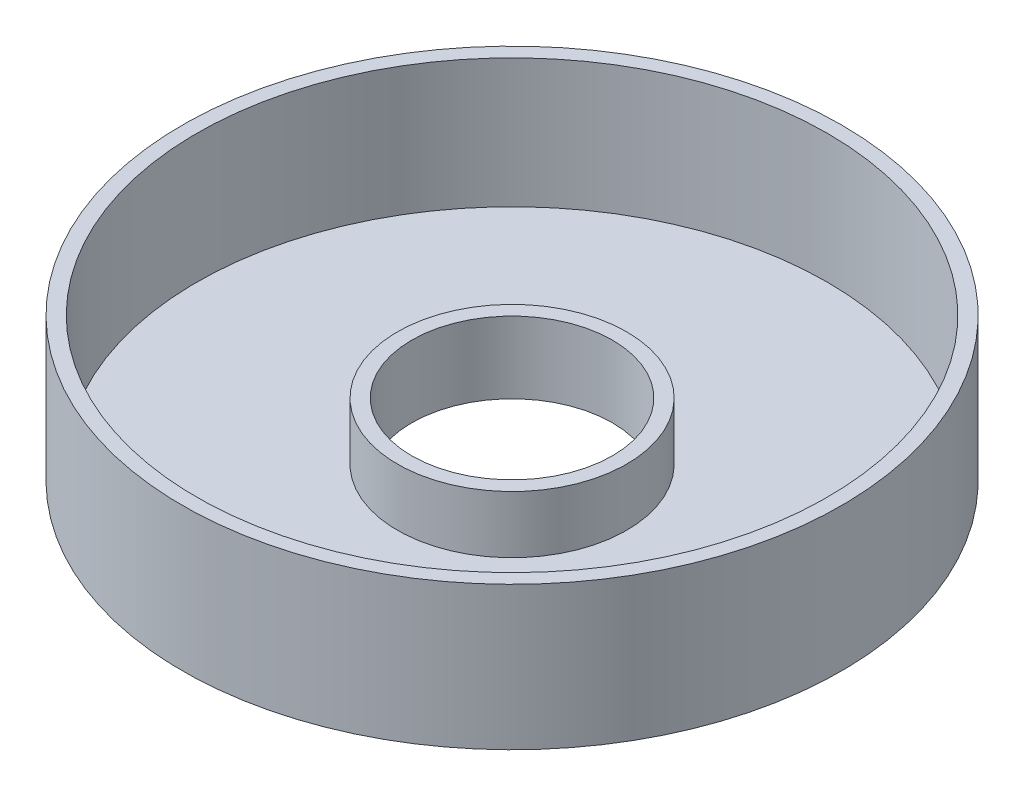
SolidWorks part; units mm, degrees
ref_plane "Front Plane" through (0, 0, 0) normal (0, 0, 1) x (1, 0, 0)
ref_plane "Top Plane" through (0, 0, 0) normal (0, 1, 0) x (1, 0, 0)
ref_plane "Right Plane" through (0, 0, 0) normal (1, 0, 0) x (0, 0, -1)
sketch "Sketch1" plane through (0, 0, 0) normal (0, 0, 1) x (1, 0, 0)
  line L0 (0, 0) -> (0, 60.4205) construction
  line L1 (-40, 25) -> (-40, 5)
  line L2 (-40, 5) -> (-110, 5)
  line L3 (-110, 5) -> (-110, 50)
  line L4 (-110, 50) -> (-115, 50)
  line L5 (-115, 50) -> (-115, 0)
  line L6 (-115, 0) -> (-35, 0)
  line L7 (-35, 0) -> (-35, 25)
  line L8 (-35, 25) -> (-40, 25)
  dimension "D1" = 35
  dimension "D2" = 5
  dimension "D3" = 25
  dimension "D4" = 110
  dimension "D5" = 5
  dimension "D6" = 50
  dimension "D7" = 5
revolve "Revolve1" add sketch "Sketch1" angle 360 about L0
